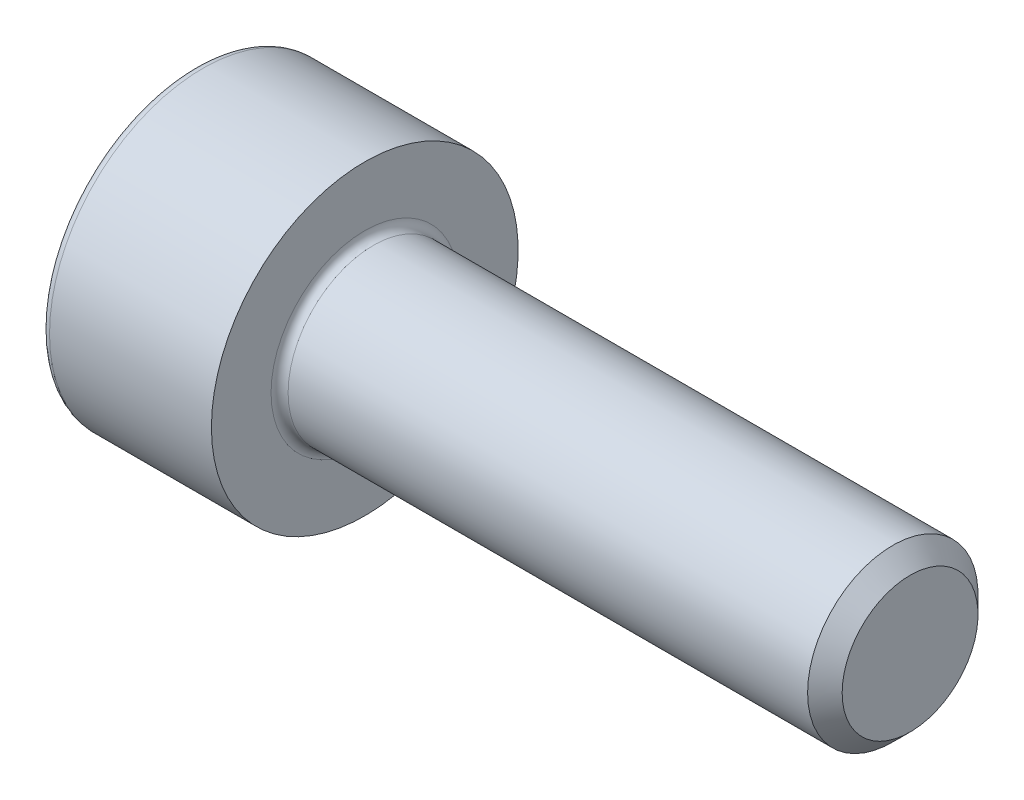
SolidWorks part; units mm, degrees
ref_plane "Front" through (0, 0, 0) normal (0, 0, 1) x (1, 0, 0)
ref_plane "Top" through (0, 0, 0) normal (0, 1, 0) x (1, 0, 0)
ref_plane "Right" through (0, 0, 0) normal (1, 0, 0) x (0, 0, -1)
sketch "Sketch1" plane through (0, 0, 0) normal (0, 0, 1) x (1, 0, 0)
  line L0 (7.7465, 1.25) -> (0.125, 1.25)
  line L1 (-2.5, 2.125) -> (-2.5, 0)
  line L2 (0, 2.25) -> (-2.375, 2.25)
  line L3 (0, 1.375) -> (0, 2.25)
  line L4 (8, 0.9965) -> (8, 0)
  line L5 (8, 0.9965) -> (7.7465, 1.25)
  line L6 (-2.5, 0) -> (0, 0) construction
  line L7 (-2.5, 0) -> (8, 0)
  arc A0 (-2.375, 2.25) -> (-2.5, 2.125) centre (-2.375, 2.125) ccw
  arc A1 (0, 1.375) -> (0.125, 1.25) centre (0.125, 1.375) ccw
  point P12 (0, 1.8125)
  dimension "D5" = 0.125
  dimension "D1" = 2.5
  dimension "D2" = 4.5
  dimension "D3" = 135
  dimension "D4" = 0.3585
  dimension "D6" = 8
  dimension "D7" = 2.5
revolve "Revolve1" add sketch "Sketch1" angle 360 about L7
sketch "Sketch2" plane through (-2.5, 0, 0) normal (-1, 0, 0) x (0, 0, 1)
  line L7 (1.025, 0.5918) -> (0, 1.1836)
  line L8 (0, 1.1836) -> (-1.025, 0.5918)
  line L9 (-1.025, 0.5918) -> (-1.025, -0.5918)
  line L10 (-1.025, -0.5918) -> (0, -1.1836)
  line L11 (0, -1.1836) -> (1.025, -0.5918)
  line L12 (1.025, -0.5918) -> (1.025, 0.5918)
  circle A0 centre (0, 0) radius 1.025 construction
  dimension "D1" = 2.05
extrude "Cut-Extrude1" cut sketch "Sketch2" against normal blind 1.1
